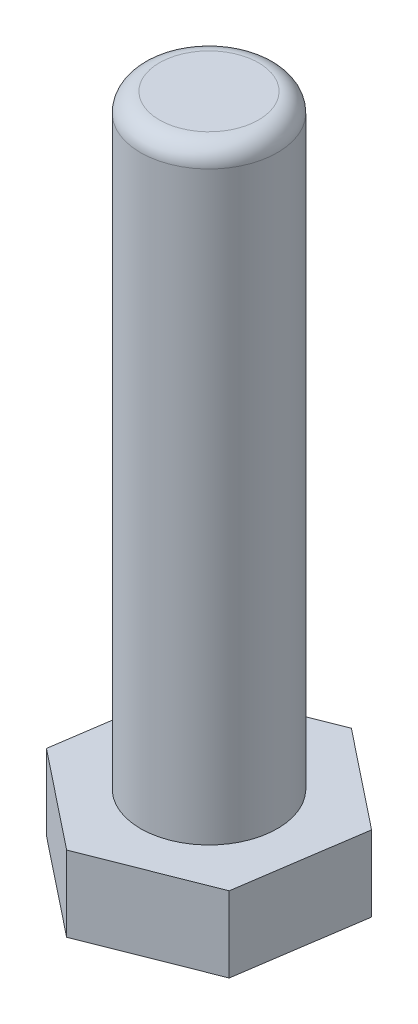
SolidWorks part; units mm, degrees
ref_plane "Plan de face" through (0, 0, 0) normal (0, 0, 1) x (1, 0, 0)
ref_plane "Plan de dessus" through (0, 0, 0) normal (0, 1, 0) x (1, 0, 0)
ref_plane "Plan de droite" through (0, 0, 0) normal (1, 0, 0) x (0, 0, -1)
sketch "Esquisse1" plane through (0, 0, 0) normal (0, 1, 0) x (1, 0, 0)
  line L1 (-10.3923, 8.2527) -> (-12.3432, -4.8736)
  line L2 (-12.3432, -4.8736) -> (-1.9509, -13.1264)
  line L3 (-1.9509, -13.1264) -> (10.3923, -8.2527)
  line L4 (10.3923, -8.2527) -> (12.3432, 4.8736)
  line L5 (12.3432, 4.8736) -> (1.9509, 13.1264)
  line L6 (1.9509, 13.1264) -> (-10.3923, 8.2527)
  circle A0 centre (0, 0) radius 11.4926 construction
  dimension "D1" = 18
extrude "Boss.-Extru.1" add sketch "Esquisse1" along normal blind 8
sketch "Esquisse2" plane through (0, 8, 0) normal (0, 1, 0) x (1, 0, 0)
  circle A0 centre (0, 0) radius 7.25
  dimension "D1" = 14.5
extrude "Boss.-Extru.2" add sketch "Esquisse2" along normal blind 64
cosmetic thread "Représentation de filetage4" parameters "D1"=25, "D2"=6.619
fillet "Congé1" radius 2 1 edges at (0, 72, 7.25)
